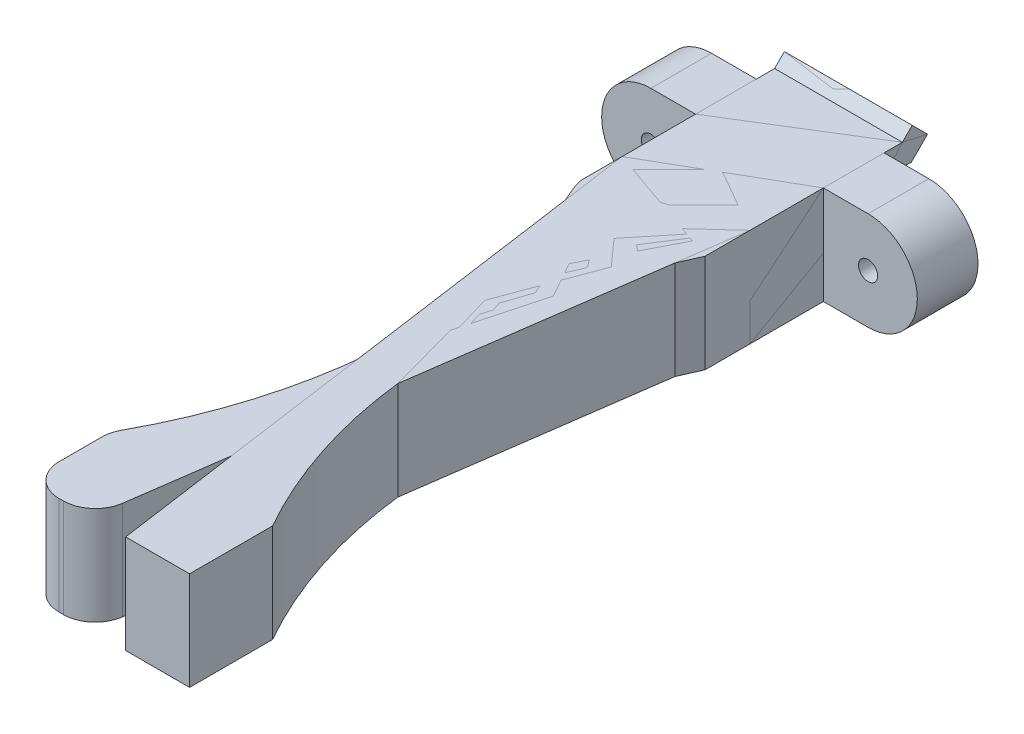
SolidWorks part; units mm, degrees
ref_plane "Front Plane" through (0, 0, 0) normal (0, 0, 1) x (1, 0, 0)
ref_plane "Top Plane" through (0, 0, 0) normal (0, 1, 0) x (1, 0, 0)
ref_plane "Right Plane" through (0, 0, 0) normal (1, 0, 0) x (0, 0, -1)
sketch "Sketch2" plane through (0, 0, 0) normal (0, 0, 1) x (1, 0, 0)
  line L0 (0, 5.9203) -> (0, 8.9503) construction
  line L1 (-5, -5.8182) -> (5, -5.8182)
  line L2 (-5, -5.8182) -> (-5, 8.9503)
  line L3 (-5, 8.9503) -> (5, 8.9503)
  line L4 (5, -5.8182) -> (5, 8.9503)
  line L7 (13.4766, 5.9203) -> (-18.5234, 5.9203) construction
  line L8 (0, -5.8182) -> (0, -2.7882) construction
  point P0 (0, 0)
  dimension "D1" = 10
extrude "Boss-Extrude1" add sketch "Sketch2" along normal blind 5
sketch "Sketch8" plane through (-5, 0, 0) normal (-1, 0, 0) x (0, 0, 1)
  line L6 (-0.15, 5.7703) -> (0, 5.7703)
  line L7 (0, 8.9503) -> (0, -5.8182) construction
  line L8 (0, 5.7703) -> (0, 4.0703)
  line L9 (0, 4.0703) -> (-0.15, 4.0703)
  line L11 (-0.15, -1.9297) -> (0, -1.9297)
  line L12 (-2.1379, 4.0703) -> (-0.15, 4.0703)
  line L13 (-0.15, 4.0703) -> (-0.15, 5.7703)
  line L14 (-0.15, 5.7703) -> (-1.4337, 5.7703)
  line L15 (-1.4337, 5.7703) -> (-2.2, 6.5366)
  line L16 (-2.2, 6.5366) -> (-3.4021, 5.3345)
  line L17 (-3.4021, 5.3345) -> (-2.1379, 4.0703)
  line L18 (-2.1379, 4.0703) -> (-0.15, 4.0703)
  line L20 (-0.15, 5.7703) -> (-1.4337, 5.7703)
  line L21 (-1.4337, 5.7703) -> (-2.2, 6.5366)
  line L22 (-2.2, 6.5366) -> (-3.4021, 5.3345)
  line L23 (-3.4021, 5.3345) -> (-2.1379, 4.0703)
  line L24 (-2.1379, -1.9297) -> (-0.15, -1.9297)
  line L25 (-0.15, -1.9297) -> (-0.15, -0.2297)
  line L26 (-0.15, -0.2297) -> (-1.4337, -0.2297)
  line L27 (-1.4337, -0.2297) -> (-2.2, 0.5366)
  line L28 (-2.2, 0.5366) -> (-3.4021, -0.6655)
  line L29 (-3.4021, -0.6655) -> (-2.1379, -1.9297)
  line L30 (-2.1379, -1.9297) -> (-0.15, -1.9297)
  line L32 (-0.15, -0.2297) -> (-1.4337, -0.2297)
  line L33 (-1.4337, -0.2297) -> (-2.2, 0.5366)
  line L34 (-2.2, 0.5366) -> (-3.4021, -0.6655)
  line L35 (-3.4021, -0.6655) -> (-2.1379, -1.9297)
  line L37 (-0.15, -0.2297) -> (0, -0.2297)
  line L38 (0, -1.9297) -> (0, -0.2297)
  dimension "D1" = 0.15
  dimension "D2" = 0.15
extrude "Boss-Extrude4" add sketch "Sketch8" against normal up to surface (10 mm away) up to face at (5, 1.566, 2.5)
sketch "Sketch9" plane through (0, 0, 0) normal (0, 0, -1) x (-1, 0, 0)
  line L4 (-5, 8.9503) -> (-5, 5.7703)
  line L5 (-5, 5.7703) -> (5, 5.7703)
  line L6 (5, 5.7703) -> (5, 8.9503)
  line L7 (5, 8.9503) -> (-5, 8.9503)
  line L8 (-5, 8.9503) -> (-5, 5.7703)
  line L10 (5, 5.7703) -> (5, 8.9503)
  line L11 (5, 8.9503) -> (-5, 8.9503)
  line L16 (5, -1.9297) -> (-5, -1.9297)
  line L17 (-5, -1.9297) -> (-5, -5.8182)
  line L18 (-5, -5.8182) -> (5, -5.8182)
  line L19 (5, -5.8182) -> (5, -1.9297)
  line L21 (-5, -1.9297) -> (-5, -5.8182)
  line L22 (-5, -5.8182) -> (5, -5.8182)
  line L23 (5, -5.8182) -> (5, -1.9297)
  line L26 (-5, 5.7703) -> (5, 5.7703)
  line L27 (5, -1.9297) -> (-5, -1.9297)
  dimension "D1" = 0
  dimension "D2" = 0
extrude "Cut-Extrude3" cut sketch "Sketch9" against normal blind 5
sketch "Sketch10" plane through (0, 5.7703, 0) normal (0, 1, 0) x (1, 0, 0)
  line L0 (-5, -5) -> (-5, -10.5)
  line L1 (-5, -10.5) -> (1.3524, -55.7)
  line L2 (1.3524, -55.7) -> (6.3524, -55.7)
  line L3 (-5, -5) -> (5, -5)
  line L4 (-120.9789, 453.7107) -> (412.3545, 453.7107) construction
  line L5 (6.3524, -55.7) -> (6.3524, -49.2)
  line L6 (5, -5) -> (5, -14)
  arc A1 (5, -14) -> (6.3524, -49.2) centre (39.6089, -30.2962) ccw
  dimension "D1" = 172
  dimension "D2" = 45.2
  dimension "D3" = 5
  dimension "D4" = 6.5
  dimension "D5" = 5.5
  dimension "D6" = 9
extrude "Boss-Extrude5" add sketch "Sketch10" against normal up to surface (7.7 mm away) up to face at (0, -1.9297, 1.4311)
ref_plane "Plane1" through (0, 0, 2.75) normal (0, 0, 1) x (1, 0, 0)
sketch "Sketch12" plane through (0, 0, 0) normal (0, 0, 1) x (1, 0, 0)
  line L0 (5, 5.7703) -> (8.5, 5.7703)
  line L1 (8.5, -1.9297) -> (5, -1.9297)
  line L2 (5, -1.9297) -> (5, 5.7703)
  line L3 (1.3524, 5.7703) -> (6.3524, 5.7703) construction
  line L4 (1.3524, -1.9297) -> (6.3524, -1.9297) construction
  line L5 (5, 5.3345) -> (5, 6.5366) construction
  line L6 (6.3524, 5.7703) -> (1.3552, 5.7703) construction
  arc A0 (8.5, 5.7703) -> (8.5, -1.9297) centre (8.5, 1.9203) cw
  circle A1 centre (8.5, 1.9203) radius 0.75
  dimension "D1" = 1.5
  dimension "D2" = 3.5
extrude "Boss-Extrude7" add sketch "Sketch12" along normal offset from surface (4.75 mm away) 2 up to plane "Plane1" offset beyond the face yes
mirror "Mirror1" about plane through (0, 0, 0) normal (1, 0, 0) of bodies 112
fillet "Fillet1" radius 2.5 4 edges at (-6.3524, 1.9203, 49.2) (-5, 1.9203, 14) (-1.3524, 1.9203, 55.7) (-6.3524, 1.9203, 55.7)
